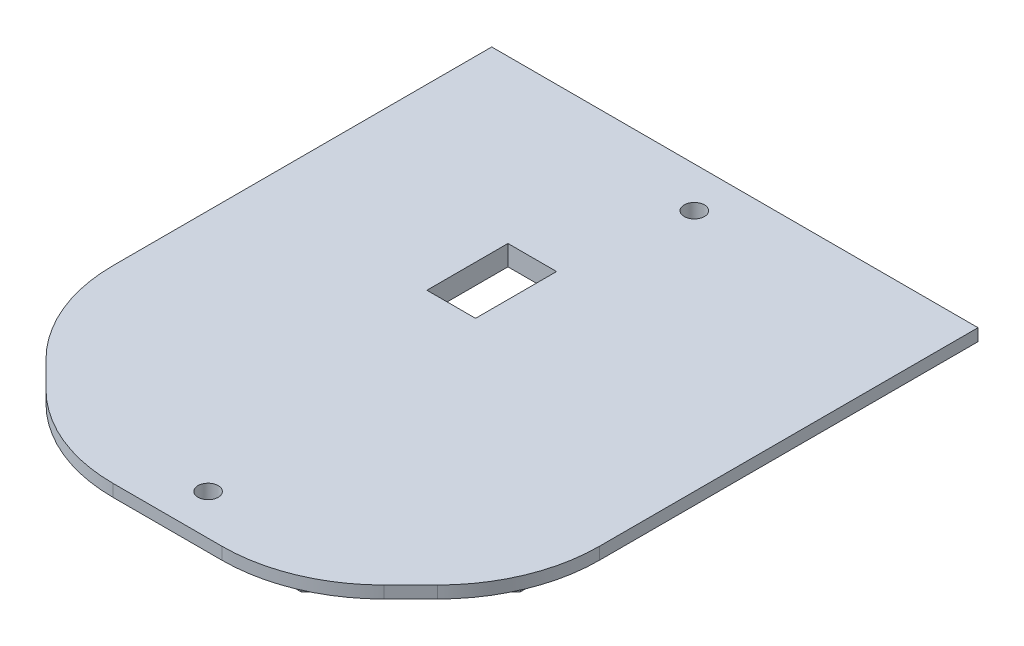
SolidWorks part; units mm, degrees
material "ABS"
ref_plane "Front Plane" through (0, 0, 0) normal (0, 0, 1) x (1, 0, 0)
ref_plane "Top Plane" through (0, 0, 0) normal (0, 1, 0) x (1, 0, 0)
ref_plane "Right Plane" through (0, 0, 0) normal (1, 0, 0) x (0, 0, -1)
sketch "Sketch1" plane through (0, 0, 0) normal (0, 1, 0) x (1, 0, 0)
  line L0 (-76.2, -50.8) -> (-38.1, -88.9)
  line L1 (-38.1, -88.9) -> (38.1, -88.9)
  line L2 (-76.2, -50.8) -> (-76.2, 88.9)
  line L3 (-76.2, 88.9) -> (76.2, 88.9)
  line L4 (76.2, -50.8) -> (76.2, 88.9)
  line L5 (-76.2, -88.9) -> (76.2, 88.9) construction
  line L6 (-76.2, 88.9) -> (76.2, -88.9) construction
  line L7 (38.1, -88.9) -> (76.2, -50.8)
  circle A0 centre (0, 76.2) radius 3.175
  circle A1 centre (0, -76.2) radius 3.175
  point P1 (0, 0)
  point P11 (0, 88.9)
  dimension "D3" = 6.35
  dimension "D1" = 152.4
  dimension "D2" = 177.8
  dimension "D4" = 12.7
  dimension "D5" = 12.7
extrude "Boss-Extrude1" add sketch "Sketch1" along normal blind 3.81
sketch "Sketch2" plane through (0, 0, 0) normal (0, -1, 0) x (1, 0, 0)
  line L0 (-69.85, 48.1697) -> (-69.85, -82.55)
  line L1 (-69.85, -82.55) -> (69.85, -82.55)
  line L2 (69.85, -82.55) -> (69.85, 48.1697)
  line L3 (69.85, 48.1697) -> (35.4697, 82.55)
  line L4 (35.4697, 82.55) -> (-35.4697, 82.55)
  line L5 (-35.4697, 82.55) -> (-69.85, 48.1697)
  line L6 (76.2, -88.9) -> (76.2, 50.8)
  line L7 (-76.2, -88.9) -> (76.2, -88.9)
  line L8 (-76.2, 50.8) -> (-76.2, -88.9)
  line L9 (-38.1, 88.9) -> (-76.2, 50.8)
  line L10 (38.1, 88.9) -> (-38.1, 88.9)
  line L11 (76.2, 50.8) -> (38.1, 88.9)
  line L12 (76.2, -88.9) -> (76.2, 50.8) construction
  line L13 (-76.2, -88.9) -> (76.2, -88.9) construction
  line L14 (-76.2, 50.8) -> (-76.2, -88.9) construction
  line L15 (-38.1, 88.9) -> (-76.2, 50.8) construction
  line L16 (38.1, 88.9) -> (-38.1, 88.9) construction
  line L17 (76.2, 50.8) -> (38.1, 88.9) construction
  circle A0 centre (0, 76.2) radius 3.175 construction
  circle A1 centre (0, -76.2) radius 3.175 construction
  circle A2 centre (0, 76.2) radius 3.175
  circle A3 centre (0, -76.2) radius 3.175
  dimension "D1" = 0
  dimension "D2" = 6.35
extrude "Boss-Extrude2" add sketch "Sketch2" along normal blind 2.54
fillet "Fillet1" radius 50.8 4 edges at (76.2, 1.905, 50.8) (38.1, 1.905, 88.9) (-38.1, 1.905, 88.9) (-76.2, 1.905, 50.8)
sketch "Sketch3" plane through (0, 3.81, 0) normal (0, 1, 0) x (1, 0, 0)
  line L0 (-50.8, 25.4) -> (50.8, 25.4) construction
  line L1 (76.2, 88.9) -> (-76.2, 88.9) construction
  line L3 (-20.32, 38.1) -> (-5.08, 38.1)
  line L4 (-20.32, 38.1) -> (-20.32, 12.7)
  line L5 (-20.32, 12.7) -> (-5.08, 12.7)
  line L6 (-5.08, 38.1) -> (-5.08, 12.7)
  line L7 (-20.32, 38.1) -> (-5.08, 12.7) construction
  line L8 (-20.32, 12.7) -> (-5.08, 38.1) construction
  circle A0 centre (-50.8, 25.4) radius 25.4 construction
  circle A1 centre (-12.7, 25.4) radius 12.7 construction
  circle A2 centre (12.7, 25.4) radius 12.7 construction
  circle A3 centre (50.8, 25.4) radius 25.4 construction
  point P8 (0, 25.4)
  point P11 (0, 88.9)
  point P12 (-12.7, 25.4)
  dimension "D2" = 50.8
  dimension "D3" = 25.4
  dimension "D1" = 101.6
  dimension "D4" = 25.4
  dimension "D5" = 15.24
  dimension "D6" = 63.5
extrude "Cut-Extrude1" cut sketch "Sketch3" against normal through all
